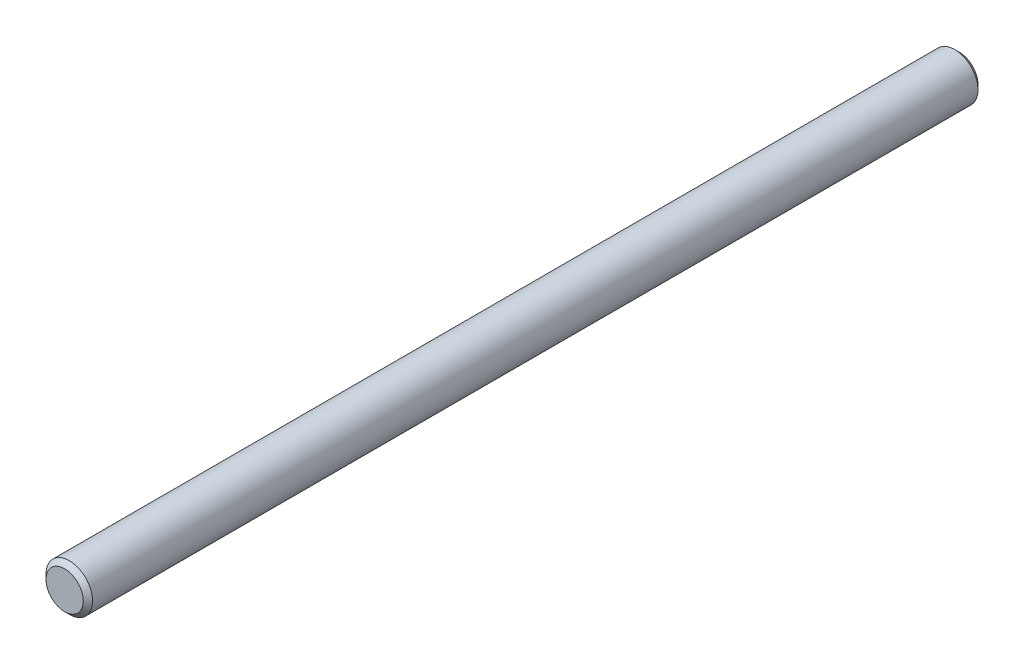
SolidWorks part; units mm, degrees
ref_plane "Front" through (0, 0, 0) normal (0, 0, 1) x (1, 0, 0)
ref_plane "Top" through (0, 0, 0) normal (0, 1, 0) x (1, 0, 0)
ref_plane "Right" through (0, 0, 0) normal (1, 0, 0) x (0, 0, -1)
sketch "Sketch1" plane through (0, 0, 0) normal (0, 0, 1) x (1, 0, 0)
  circle A0 centre (0, 0) radius 7.9375
  dimension "dia" = 15.875
extrude "Extrude1" add sketch "Sketch1" along normal mid plane 304.8
sketch "Sketch2" plane through (0, 0, 0) normal (1, 0, 0) x (0, 0, -1)
  line L0 (-152.4, 7.9375) -> (-152.4, -7.9375) construction
  line L1 (152.4, 7.9375) -> (152.4, -7.9375) construction
  line L2 (152.4, 7.9375) -> (149.9, 7.9375) construction
  line L3 (152.4, 7.9375) -> (-152.4, 7.9375) construction
  line L4 (-152.4, 7.9375) -> (-149.9, 7.9375) construction
  line L5 (65.2, 7.9375) -> (67.2, 7.9375) construction
  line L7 (-149.9, 7.9375) -> (-111.8, 7.9375) construction
  line L8 (-111.8, 7.9375) -> (-109.8, 7.9375) construction
  line L11 (-109.8, 7.9375) -> (-99.8, 7.9375) construction
  line L12 (-99.8, 7.9375) -> (-97.9, 7.9375) construction
  line L13 (-99.8, 7.9375) -> (65.2, 7.9375) construction
  line L14 (152.4, 7.9375) -> (-152.4, 7.9375) construction
  point P0 (-152.4, 7.9375)
  point P1 (152.4, 7.9375)
  dimension "D1" = 2.5
  dimension "D2" = 2.5
  dimension "D3" = 165
  dimension "D4" = 2
  dimension "D5" = 38.1
  dimension "D6" = 2
  dimension "D9" = 10
  dimension "D10" = 1.9
chamfer "Chamfer1" distance 1.5875 angle 45 2 edges at (7.9375, 0, -152.4) (7.9375, 0, 152.4)
equation "\"D1@Chamfer1\" = \"dia@Sketch1\" * .1"
